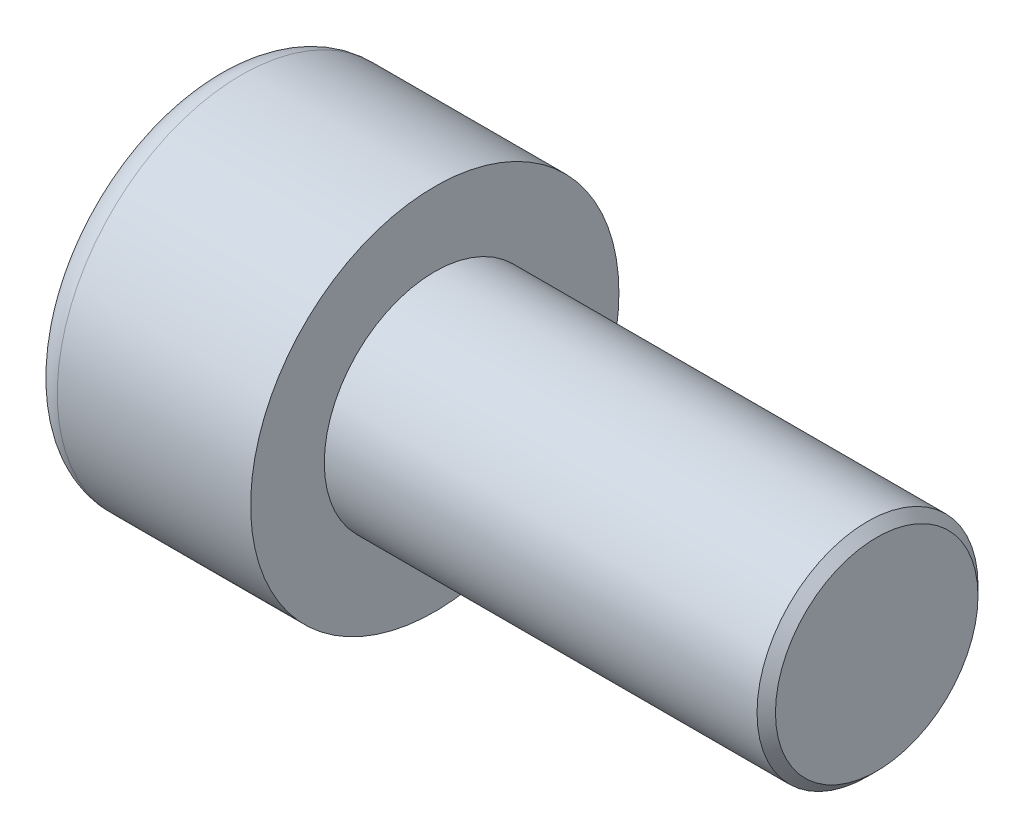
SolidWorks part; units mm, degrees
ref_plane "Front" through (0, 0, 0) normal (0, 0, 1) x (1, 0, 0)
ref_plane "Top" through (0, 0, 0) normal (0, 1, 0) x (1, 0, 0)
ref_plane "Right" through (0, 0, 0) normal (1, 0, 0) x (0, 0, -1)
sketch "Sketch1" plane through (0, 0, 0) normal (1, 0, 0) x (0, 0, -1)
  circle A0 centre (0, 0) radius 5
  dimension "dk" = 10
extrude "BaseHead" add sketch "Sketch1" along normal blind 6
sketch "Sketch2" plane through (6, 0, 0) normal (1, 0, 0) x (0, 0, -1)
  circle A0 centre (0, 0) radius 3
  dimension "d" = 6
extrude "BaseBody" add sketch "Sketch2" along normal blind 12
cosmetic thread "ThreadCosmetic1" parameters "b"=12, "D2"=4.917
sketch "Sketch3" plane through (0, 0, 0) normal (1, 0, 0) x (0, 0, -1)
  line L1 (2.8868, 0) -> (1.4434, 2.5)
  line L2 (1.4434, 2.5) -> (-1.4434, 2.5)
  line L3 (-1.4434, 2.5) -> (-2.8868, 0)
  line L4 (-2.8868, 0) -> (-1.4434, -2.5)
  line L5 (-1.4434, -2.5) -> (1.4434, -2.5)
  line L6 (1.4434, -2.5) -> (2.8868, 0)
  circle A0 centre (0, 0) radius 2.5 construction
  dimension "s" = 5
  dimension "e" = 5.7735
extrude "HexagonSocket" cut sketch "Sketch3" along normal blind 3
sketch "Sketch4" plane through (-4.1961, 0.75, 0) normal (0, 0, 1) x (-1, 0, 0)
  line L0 (-7.1961, 3.25) -> (-8.6395, 0.75)
  line L2 (-8.6395, 0.75) -> (-7.1961, 0.75)
  line L3 (-7.1961, 0.75) -> (-7.1961, 3.25)
  line L4 (-5.0351, 0.75) -> (0.839, 0.75) construction
  line L5 (-22.1961, 0.75) -> (-10.1961, 0.75) construction
  line L6 (-10.1961, 0.75) -> (-4.1961, 0.75) construction
  dimension "m" = 60
revolve "Cut-Revolve1" cut sketch "Sketch4" angle 360 about L4
fillet "HeadFillet" [suppressed] radius 0.25
fillet "TopFillet" radius 0.75 1 edges at (0, 0, -5)
chamfer "Chamfer1" distance 0.25 angle 45 1 edges at (18, 0, -3)
sketch "Sketch5" plane through (0, 0, 0) normal (0, 0, 1) x (1, 0, 0)
  line L0 (17.75, 2.531) -> (18.0208, 3)
  line L1 (18.0208, 3) -> (18.0208, 3.5415)
  line L2 (18.0208, 3.5415) -> (17.4793, 3.5415)
  line L3 (17.4793, 3.5415) -> (17.4793, 3)
  line L4 (17.4793, 3) -> (17.75, 2.531)
  line L5 (0, 0) -> (7.8886, 0) construction
  line L6 (17.75, -3) -> (17.75, 3) construction
  dimension "D1" = 6
  dimension "D2" = 0.5415
revolve "Cut-Revolve10" [suppressed] cut sketch "Sketch5" angle 360 about L5
pattern_linear "LPattern10" [suppressed] count 18 spacing 0.6498 along (1, 0, 0)
equation "\"r1@TopFillet\" = \"d@Sketch2\" / 8"
equation "\"D1@Chamfer1\" = \"r@HeadFillet\""
equation "\"D1@Sketch5\" = \"d@Sketch2\""
equation "\"D2@Sketch5\" =  ( \"d@Sketch2\" - \"D2@ThreadCosmetic1\" )  / 2"
equation "\"D3@LPattern10\" = \"D2@Sketch5\" * 1.2"
equation "\"D1@LPattern10\" = \"b@ThreadCosmetic1\" / \"D3@LPattern10\""
